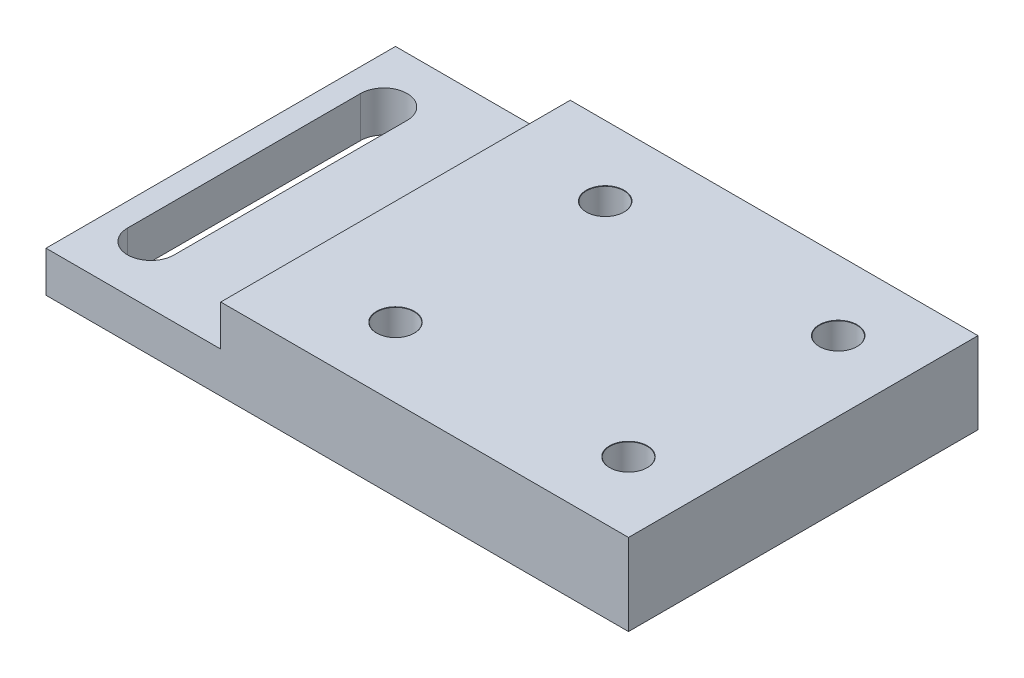
SolidWorks part; units mm, degrees
ref_plane "前视基准面" through (0, 0, 0) normal (0, 0, 1) x (1, 0, 0)
ref_plane "上视基准面" through (0, 0, 0) normal (0, 1, 0) x (1, 0, 0)
ref_plane "右视基准面" through (0, 0, 0) normal (1, 0, 0) x (0, 0, -1)
sketch "Sketch1" plane through (0, 0, 0) normal (0, 1, 0) x (1, 0, 0)
  line L1 (-25, -15) -> (25, -15)
  line L2 (-25, -15) -> (-25, 15)
  line L3 (-25, 15) -> (25, 15)
  line L4 (25, -15) -> (25, 15)
  line L5 (-25, -15) -> (25, 15) construction
  line L6 (-25, 15) -> (25, -15) construction
  point P0 (0, 0)
  dimension "D1" = 50
  dimension "D2" = 30
extrude "Boss-Extrude1" add sketch "Sketch1" along normal blind 7
sketch "Sketch2" plane through (0, 7, 0) normal (0, 1, 0) x (1, 0, 0)
  line L0 (25, 15) -> (-25, 15) construction
  line L1 (-25, -15) -> (-10, -15)
  line L2 (-25, -15) -> (-25, 15)
  line L3 (-25, 15) -> (-10, 15)
  line L4 (-10, -15) -> (-10, 15)
  dimension "D1" = 15
extrude "Cut-Extrude1" cut sketch "Sketch2" against normal blind 3.5
sketch "Sketch3" plane through (0, 3.5, 0) normal (0, 1, 0) x (1, 0, 0)
  line L0 (-21, 10) -> (-21, -10) construction
  line L1 (-19, 10) -> (-19, -10)
  line L2 (-23, 10) -> (-23, -10)
  line L3 (-25, 15) -> (-25, -15) construction
  line L4 (-25, -15) -> (-10, -15) construction
  arc A0 (-19, 10) -> (-23, 10) centre (-21, 10) ccw
  arc A1 (-23, -10) -> (-19, -10) centre (-21, -10) ccw
  point P2 (-21, 0)
  point P11 (-21.1023, -3.7169)
  dimension "D1" = 20
  dimension "D2" = 4
  dimension "D3" = 5
  dimension "D4" = 4
extrude "Cut-Extrude2" cut sketch "Sketch3" against normal through all
hole_wizard "M3 Clearance Hole1" positions "Sketch4" profile "Sketch5" hole size "M3" standard "GB" end condition through all
sketch "Sketch4" plane through (0, 7, 0) normal (0, 1, 0) x (1, 0, 0)
  line L0 (-10, -15) -> (25, -15) construction
  line L1 (25, -15) -> (25, 15) construction
  point P0 (-1, 9)
  point P2 (-1, -9)
  point P4 (19, 9)
  point P6 (19, -9)
  point P9 (-3.0344, -7.1286)
  point P10 (18.932, 8.2629)
  point P15 (19, 9)
  point P16 (0, 0)
  point P17 (-1, -6.3379)
  point P18 (-1, -9)
  point P19 (0, 0)
  point P20 (19, 9)
  point P21 (-1, 9)
  point P22 (0, 0)
  point P23 (-1, 9)
  point P24 (-1, -9)
  point P25 (19, -9)
  dimension "D1" = 20
  dimension "D2" = 20
  dimension "D3" = 18
  dimension "D4" = 6
  dimension "D5" = 6
sketch "Sketch5" plane through (-1, 7, -9) normal (1, 0, 0) x (0, 0, 1)
  line L0 (0, 0) -> (0, 7)
  line L1 (0, 7) -> (1.6, 7)
  line L2 (1.6, 7) -> (1.6, 0.025)
  line L3 (1.6, 0.025) -> (1.625, 0)
  line L5 (1.625, 0) -> (0, 0)
  line L6 (-1.6, 0.025) -> (-1.625, 0) construction
  line L11 (0, -6.35) -> (0, 107.95) construction
  dimension "Thru Hole Dia." = 3.2
  dimension "Thru Hole Depth" = 7
  dimension "Near C'Sink Dia." = 3.25
  dimension "Near C'Sink Angle" = 90
